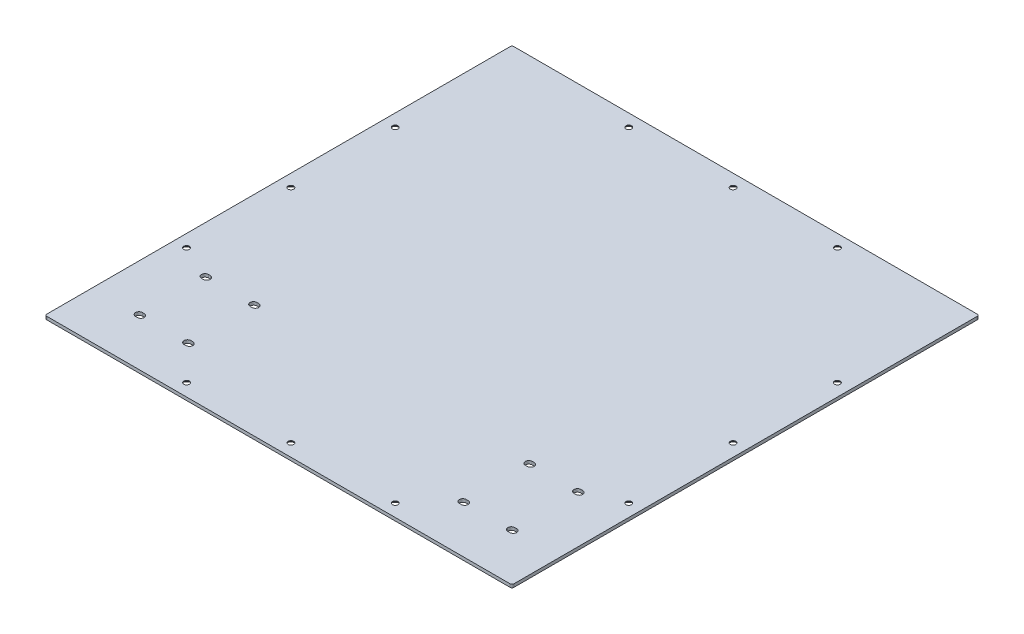
SolidWorks part; units mm, degrees
material "6063-T5"
ref_plane "Front Plane" through (0, 0, 0) normal (0, 0, 1) x (1, 0, 0)
ref_plane "Top Plane" through (0, 0, 0) normal (0, 1, 0) x (1, 0, 0)
ref_plane "Right Plane" through (0, 0, 0) normal (1, 0, 0) x (0, 0, -1)
sketch "Sketch1" plane through (0, 0, 0) normal (0, 1, 0) x (1, 0, 0)
  line L1 (0, 0) -> (750, 0)
  line L2 (0, 0) -> (0, -750)
  line L3 (0, -750) -> (750, -750)
  line L4 (750, 0) -> (750, -750)
  line L5 (0, 0) -> (750, -750) construction
  line L6 (0, -750) -> (750, 0) construction
  point P4 (375, -375)
  dimension "D1" = 750
  dimension "D2" = 750
extrude "Boss-Extrude1" add sketch "Sketch1" along normal blind 5
sketch "Sketch2" plane through (0, 0, 0) normal (0, -1, 0) x (1, 0, 0)
  line L0 (750, 0) -> (0, 0) construction
  line L1 (0, 750) -> (40, 750) construction
  line L2 (0, 750) -> (0, 0) construction
  line L3 (0, 0) -> (40, 0) construction
  line L4 (40, 750) -> (40, 0) construction
  line L5 (0, 750) -> (40, 0) construction
  line L6 (0, 0) -> (40, 750) construction
  line L7 (750, 750) -> (750, 0) construction
  line L8 (0, 750) -> (750, 750) construction
  line L9 (0, 750) -> (0, 710) construction
  line L10 (0, 710) -> (750, 710) construction
  line L11 (750, 750) -> (750, 710) construction
  line L12 (0, 750) -> (750, 710) construction
  line L13 (0, 710) -> (750, 750) construction
  line L14 (74.5, 673.5) -> (77.5, 673.5) construction
  line L15 (0, 750) -> (150, 750)
  line L16 (0, 750) -> (0, 571)
  line L17 (0, 571) -> (150, 571) construction
  line L18 (150, 750) -> (150, 571) construction
  line L19 (0, 750) -> (150, 571) construction
  line L20 (0, 571) -> (150, 750) construction
  line L21 (74.5, 679) -> (77.5, 679)
  line L22 (74.5, 668) -> (77.5, 668)
  line L23 (152.5, 673.5) -> (155.5, 673.5) construction
  line L24 (152.5, 679) -> (155.5, 679)
  line L25 (152.5, 668) -> (155.5, 668)
  line L26 (152.5, 567.5) -> (155.5, 567.5) construction
  line L27 (152.5, 573) -> (155.5, 573)
  line L28 (152.5, 562) -> (155.5, 562)
  line L29 (74.5, 567.5) -> (77.5, 567.5) construction
  line L30 (74.5, 573) -> (77.5, 573)
  line L31 (74.5, 562) -> (77.5, 562)
  line L33 (0, 750) -> (154, 750)
  line L34 (0, 750) -> (0, 690)
  line L35 (0, 690) -> (154, 690)
  line L36 (154, 750) -> (154, 690)
  line L37 (0, 750) -> (154, 690) construction
  line L38 (0, 690) -> (154, 750) construction
  arc A0 (74.5, 679) -> (74.5, 668) centre (74.5, 673.5) ccw
  arc A1 (77.5, 668) -> (77.5, 679) centre (77.5, 673.5) ccw
  arc A2 (152.5, 679) -> (152.5, 668) centre (152.5, 673.5) ccw
  arc A3 (155.5, 668) -> (155.5, 679) centre (155.5, 673.5) ccw
  arc A4 (152.5, 573) -> (152.5, 562) centre (152.5, 567.5) ccw
  arc A5 (155.5, 562) -> (155.5, 573) centre (155.5, 567.5) ccw
  arc A6 (74.5, 573) -> (74.5, 562) centre (74.5, 567.5) ccw
  arc A7 (77.5, 562) -> (77.5, 573) centre (77.5, 567.5) ccw
  point P4 (20, 375)
  point P11 (375, 730)
  point P17 (75, 660.5)
  point P20 (76, 673.5)
  point P26 (69, 673.5)
  point P27 (83, 673.5)
  point P32 (154, 673.5)
  point P39 (154, 567.5)
  point P46 (76, 567.5)
  point P54 (77, 720)
  dimension "D6" = 14
  dimension "D1" = 40
  dimension "D2" = 40
  dimension "D3" = 179
  dimension "D4" = 150
  dimension "D5" = 29
  dimension "D7" = 11
  dimension "D8" = 31
  dimension "D9" = 2
  dimension "D11" = 60
  dimension "D12" = 95
  dimension "D10" = 2
hole_wizard "CSK for M8 Flat Head Machine Screw1" positions "Sketch3" profile "Sketch4" countersink size "M8" standard "ANSI Metric" end condition through all
sketch "Sketch3" plane through (0, 0, 0) normal (0, -1, 0) x (-1, 0, 0)
  point P0 (-20, -375)
  point P3 (-20, -542.5)
  point P5 (-20, -207.5)
  point P6 (-375, -730)
  point P9 (-542.5, -730)
  point P11 (-207.5, -730)
  dimension "D1" = 167.5
  dimension "D2" = 167.5
  dimension "D3" = 167.5
  dimension "D4" = 167.5
sketch "Sketch4" plane through (20, 0, 375) normal (1, 0, 0) x (0, 0, -1)
  line L0 (0, 0) -> (0, 5)
  line L1 (0, 5) -> (4.5, 5)
  line L2 (4.5, 5) -> (4.5, 4.15)
  line L3 (4.5, 4.15) -> (8.65, 0)
  line L5 (8.65, 0) -> (0, 0)
  line L6 (-4.5, 4.15) -> (-8.65, 0) construction
  line L11 (0, -6.35) -> (0, 107.95) construction
  dimension "Thru Hole Dia." = 9
  dimension "Thru Hole Depth" = 5
  dimension "Near C'Sink Dia." = 17.3
  dimension "Near C'Sink Angle" = 90
ref_plane "Plane1" through (375, 0, 0) normal (1, 0, 0) x (0, 0, -1)
mirror "Mirror1" about plane through (375, 0, 0) normal (1, 0, 0) of "CSK for M8 Flat Head Machine Screw1"
ref_plane "Plane2" through (0, 0, 375) normal (0, 0, -1) x (-1, 0, 0)
mirror "Mirror2" about plane through (0, 0, 375) normal (0, 0, -1) of "Mirror1"
fillet "Fillet1" radius 3 4 edges at (750, 2.5, 0) (0, 2.5, 0) (0, 2.5, 750) (750, 2.5, 750)
extrude "Cut-Extrude1" cut sketch "Sketch2" against normal through all contours L25 A3 L24 A2 | L22 A1 L21 A0 | L31 A7 L30 A6 | L28 A5 L27 A4
pattern_linear "LPattern1" count 2 spacing 520 along (1, 0, 0) of "Cut-Extrude1"
